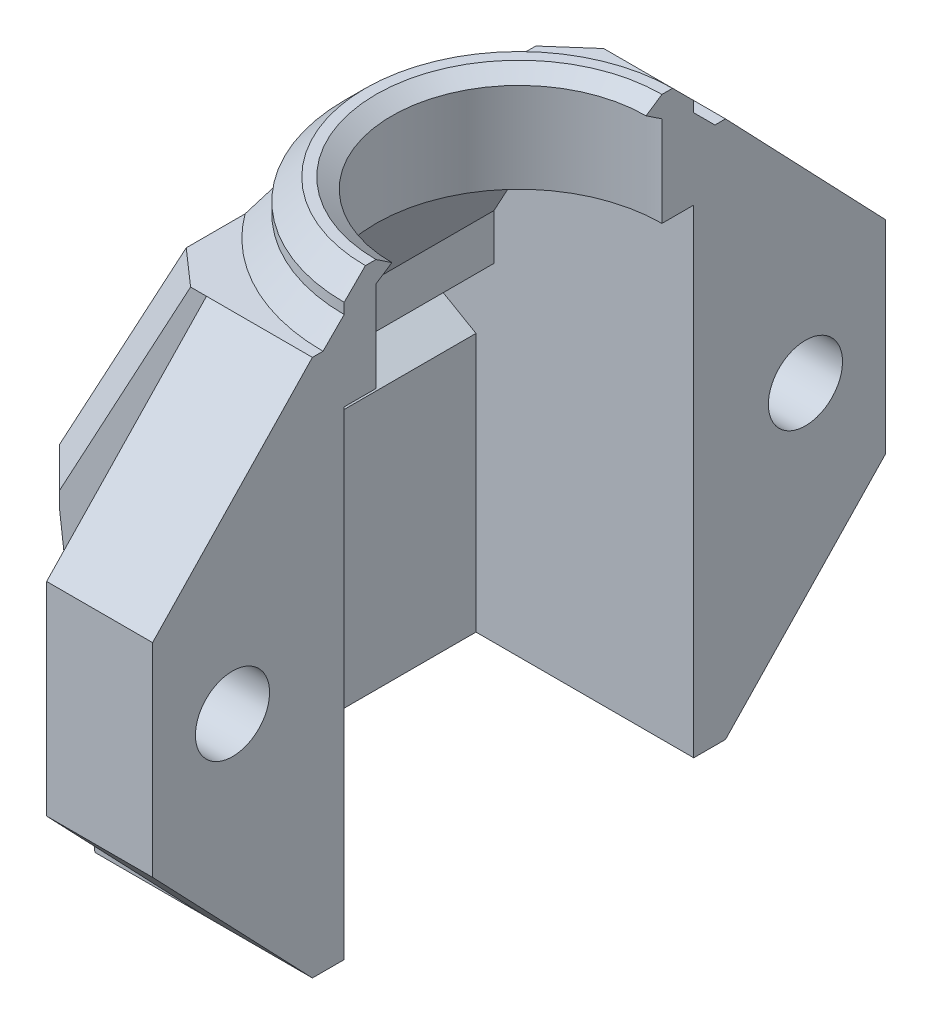
SolidWorks part; units mm, degrees
ref_plane "Front Plane" through (0, 0, 0) normal (0, 0, 1) x (1, 0, 0)
ref_plane "Top Plane" through (0, 0, 0) normal (0, 1, 0) x (1, 0, 0)
ref_plane "Right Plane" through (0, 0, 0) normal (1, 0, 0) x (0, 0, -1)
sketch "Sketch1" plane through (0, 0, 0) normal (0, 0, 1) x (1, 0, 0)
  line L0 (-10.279, -12.6848) -> (-10.279, -0.4735)
  line L1 (-11.9441, 0.4878) -> (-11.9441, 1.6425)
  line L2 (11.779, -12.6848) -> (-11.779, -12.6848)
  line L3 (-9.4275, 2.8152) -> (-9.4275, 4.9732)
  line L4 (-9.913, 2.8152) -> (-9.4275, 2.8152)
  line L5 (-9.913, 2.8152) -> (-11.9441, 1.6425)
  line L6 (-10.279, -0.4735) -> (-11.9441, 0.4878)
  line L7 (-6.75, 9.9108) -> (-9.4275, 4.9732)
  line L8 (9.913, 2.8152) -> (9.4275, 2.8152)
  line L9 (10.279, -12.6848) -> (10.279, -0.4735)
  line L10 (9.913, 2.8152) -> (11.9441, 1.6425)
  line L11 (11.9441, 0.4878) -> (11.9441, 1.6425)
  line L12 (9.4275, 2.8152) -> (9.4275, 4.9732)
  line L13 (10.279, -0.4735) -> (11.9441, 0.4878)
  line L14 (6.75, 9.9108) -> (9.4275, 4.9732)
  line L15 (-6.75, 9.9108) -> (6.75, 9.9108)
  line L16 (0, 12.6848) -> (0, -12.6848) construction
  line L22 (-7.4562, 12.6848) -> (7.4562, 12.6848)
  line L23 (-13.4441, 0.4878) -> (-13.4441, 1.6425)
  line L24 (-11.779, -12.6848) -> (-13.4441, 0.4878)
  line L25 (-7.4562, 12.6848) -> (-13.4441, 1.6425)
  line L26 (13.4441, 0.4878) -> (13.4441, 1.6425)
  line L27 (7.4562, 12.6848) -> (13.4441, 1.6425)
  line L28 (11.779, -12.6848) -> (13.4441, 0.4878)
extrude "Boss-Extrude1" add sketch "Sketch1" along normal blind 19.5 contours L2 L28 L26 L27 L22 L25 L23 L24 L0 L6 L1 L5 L4 L3 L7 L15 L14 L12 L8 L10 L11 L13 L9
sketch "Sketch6" plane through (0, 0, 19.5) normal (0, 0, 1) x (1, 0, 0)
  line L0 (0, 12.6848) -> (-7.4562, 12.6848)
  line L1 (-7.4562, 12.6848) -> (-13.4441, 1.6425)
  line L2 (-13.4441, 1.6425) -> (-13.4441, 0.4878)
  line L3 (-13.4441, 0.4878) -> (-11.779, -12.6848)
  line L4 (-11.779, -12.6848) -> (0, -12.6848)
  line L5 (0, -12.6848) -> (0, 12.6848)
extrude "Boss-Extrude5" add sketch "Sketch6" against normal blind 1.5
sketch "Sketch7" plane through (0, 0, 0) normal (0, 0, -1) x (-1, 0, 0)
  line L0 (0, 12.6848) -> (0, -12.6848)
  line L1 (0, -12.6848) -> (11.779, -12.6848)
  line L2 (11.779, -12.6848) -> (13.4441, 0.4878)
  line L3 (13.4441, 0.4878) -> (13.4441, 1.6425)
  line L4 (13.4441, 1.6425) -> (7.4562, 12.6848)
  line L5 (7.4562, 12.6848) -> (0, 12.6848)
extrude "Boss-Extrude6" add sketch "Sketch7" against normal blind 1.5
sketch "Sketch8" plane through (0, 12.6848, 0) normal (0, 1, 0) x (1, 0, 0)
  line L0 (0, -19.5) -> (0, 0) construction
  circle A0 centre (0, -9.75) radius 6.75
  dimension "D1" = 13.5
extrude "Cut-Extrude2" cut sketch "Sketch8" against normal through all
sketch "Sketch9" plane through (0, 12.6848, 0) normal (0, 1, 0) x (1, 0, 0)
  line L0 (0, -1.5) -> (0, -3)
  line L1 (0, -16.5) -> (0, -18)
  arc A0 (0, -3) -> (0, -16.5) centre (0, -9.75) ccw
  arc A1 (0, -1.5) -> (0, -18) centre (0, -9.75) ccw
  circle A3 centre (0, -9.75) radius 6.75 construction
  circle A4 centre (0, -9.75) radius 8.25 construction
  point P1 (8.25, -9.75)
  point P12 (6.4551, -7.7765)
  dimension "D1" = 1.5
extrude "Boss-Extrude7" add sketch "Sketch9" along normal mid plane 5
sketch "Sketch10" plane through (0, 0, 0) normal (1, 0, 0) x (0, 0, -1)
  line L0 (-19.5, 12.6848) -> (-27.0438, 4.7969)
  line L1 (-20.3969, 1.6599) -> (-23.2719, 3.3198)
  line L2 (-23.2719, 3.3198) -> (-26.1469, 1.6599)
  line L3 (-26.1469, 1.6599) -> (-26.1469, -1.6599)
  line L4 (-26.1469, -1.6599) -> (-23.2719, -3.3198)
  line L5 (-23.2719, -3.3198) -> (-20.3969, -1.6599)
  line L6 (-20.3969, -1.6599) -> (-20.3969, 1.6599)
  line L7 (-9.75, 15.1848) -> (-9.75, -12.6848) construction
  line L8 (-27.0438, -4.7969) -> (-19.5, -12.6848)
  line L9 (-27.0438, 0) -> (-19.5, 0) construction
  line L10 (-19.5, 12.6848) -> (-19.5, -12.6848)
  line L11 (-27.0438, 4.7969) -> (-27.0438, -4.7969)
  line L12 (-3, 15.1848) -> (-16.5, 15.1848) construction
  line L13 (-18, -12.6848) -> (-1.5, -12.6848) construction
  line L14 (-27.0438, 4.7969) -> (-19.5, 12.6848)
  line L15 (-23.2719, 3.3198) -> (-20.3969, 1.6599)
  line L16 (-26.1469, 1.6599) -> (-23.2719, 3.3198)
  line L17 (-23.2719, -3.3198) -> (-26.1469, -1.6599)
  line L18 (-20.3969, -1.6599) -> (-23.2719, -3.3198)
  line L19 (-19.5, -12.6848) -> (-27.0438, -4.7969)
  line L20 (7.5438, 0) -> (0, 0) construction
  line L21 (0, -12.6848) -> (7.5438, -4.7969)
  line L22 (0.8969, -1.6599) -> (3.7719, -3.3198)
  line L23 (3.7719, -3.3198) -> (6.6469, -1.6599)
  line L24 (6.6469, 1.6599) -> (3.7719, 3.3198)
  line L25 (3.7719, 3.3198) -> (0.8969, 1.6599)
  line L26 (7.5438, 4.7969) -> (0, 12.6848)
  line L27 (7.5438, 4.7969) -> (7.5438, -4.7969)
  line L28 (0, 12.6848) -> (0, -12.6848)
  line L29 (7.5438, -4.7969) -> (0, -12.6848)
  line L30 (0.8969, -1.6599) -> (0.8969, 1.6599)
  line L31 (3.7719, -3.3198) -> (0.8969, -1.6599)
  line L32 (6.6469, -1.6599) -> (3.7719, -3.3198)
  line L33 (6.6469, 1.6599) -> (6.6469, -1.6599)
  line L34 (3.7719, 3.3198) -> (6.6469, 1.6599)
  line L35 (0.8969, 1.6599) -> (3.7719, 3.3198)
  line L36 (0, 12.6848) -> (7.5438, 4.7969)
  circle A0 centre (-23.2719, 0) radius 1.75
  circle A1 centre (-23.2719, 0) radius 2.875 construction
  circle A2 centre (3.7719, 0) radius 2.875 construction
  circle A3 centre (3.7719, 0) radius 1.75
  line M3 (-19.5, 12.6848) -> (-19.5, -12.6848)
  dimension "D1" = 3.5
  dimension "D2" = 5.75
extrude "Boss-Extrude8" add sketch "Sketch10" against normal blind 5 contours L0 L11 L8 L6 L5 L4 L3 L2 L1 M3 | L5 L6 L1 L2 L3 L4 A0 | L33 L24 L25 L30 L22 L23 A3 | L26 L28 L21 L27 L24 L33 L23 L22 L30 L25
chamfer "Chamfer1" distance 1.5 angle 45 6 edges at (-12.6115, -6.0985, 19.5) (-13.4441, 1.0652, 19.5) (-10.4501, 7.1637, 19.5) (-12.6115, -6.0985, 0) (-13.4441, 1.0652, 0) (-10.4501, 7.1637, 0)
sketch "Sketch11" plane through (-5, 0, 0) normal (-1, 0, 0) x (0, 0, 1)
  line L27 (0, 12.6848) -> (-7.5438, 4.7969) construction
  line L59 (0, 12.6848) -> (-7.5438, 4.7969)
  circle A1 centre (-3.7719, 0) radius 1.75 construction
  circle A2 centre (23.2719, 0) radius 1.75
  circle A3 centre (-3.7719, 0) radius 1.75
  circle A4 centre (-3.7719, 0) radius 2.875
  circle A5 centre (23.2719, 0) radius 2.875
  circle M1 centre (-3.7719, 0) radius 1.75
  dimension "D1" = 5.75
chamfer "Chamfer2" distance 1 angle 45 1 edges at (-8.25, 15.1848, 9.75)
extrude "Cut-Extrude4" cut sketch "Sketch11" against normal blind 2.5 contours A4 M1 | A5 A2
sketch "Sketch12" plane through (0, 0, 0) normal (1, 0, 0) x (0, 0, -1)
  line L0 (-16.5, 15.1848) -> (-16.5, 14.1848)
  line L1 (-16.5, 15.1848) -> (-16.5, 9.9108) construction
  line L2 (-16.5, 14.6848) -> (-15.75, 14.6848) construction
  line L3 (-16.5, 15.1848) -> (-15.75, 14.6848)
  line L4 (-15.75, 14.6848) -> (-16.5, 14.1848)
  line L5 (-9.75, 15.1848) -> (-9.75, -12.6848) construction
  line L6 (-3, 15.1848) -> (-16.5, 15.1848) construction
  line L7 (-18, -12.6848) -> (-1.5, -12.6848) construction
revolve "Revolve1" add sketch "Sketch12" angle 180 about L5
chamfer "Chamfer3" distance 1 angle 45 1 edges at (-4.4121, 12.6848, 2.7789)
